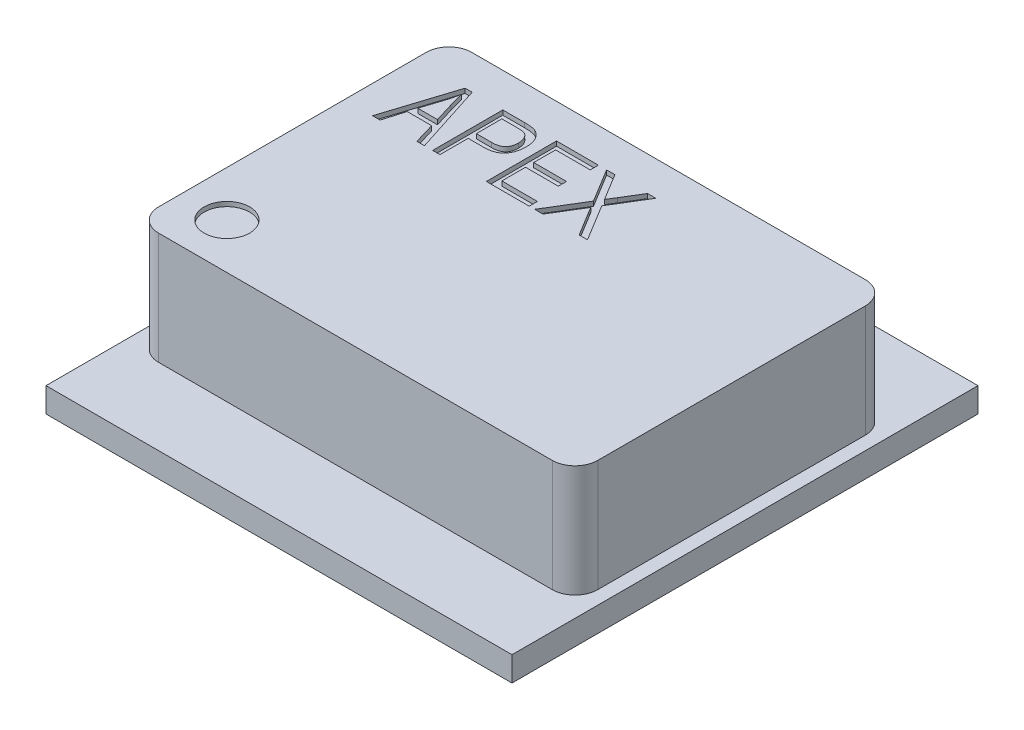
SolidWorks part; units mm, degrees
ref_plane "Front Plane" through (0, 0, 0) normal (0, 0, 1) x (1, 0, 0)
ref_plane "Top Plane" through (0, 0, 0) normal (0, 1, 0) x (1, 0, 0)
ref_plane "Right Plane" through (0, 0, 0) normal (1, 0, 0) x (0, 0, -1)
sketch "Sketch1" plane through (0, 0, 0) normal (0, 1, 0) x (1, 0, 0)
  line L1 (-5.12, -5.12) -> (5.12, -5.12)
  line L2 (-5.12, -5.12) -> (-5.12, 5.12)
  line L3 (-5.12, 5.12) -> (5.12, 5.12)
  line L4 (5.12, -5.12) -> (5.12, 5.12)
  line L5 (-5.12, -5.12) -> (5.12, 5.12) construction
  line L6 (-5.12, 5.12) -> (5.12, -5.12) construction
  point P0 (0, 0)
  dimension "D1" = 10.24
  dimension "D2" = 10.24
extrude "Boss-Extrude1" add sketch "Sketch1" along normal blind 0.54
sketch "Sketch2" plane through (0, 0.54, 0) normal (0, 1, 0) x (1, 0, 0)
  line L1 (-4.825, -3.44) -> (4.825, -3.44)
  line L2 (-4.825, -3.44) -> (-4.825, 3.44)
  line L3 (-4.825, 3.44) -> (4.825, 3.44)
  line L4 (4.825, -3.44) -> (4.825, 3.44)
  line L5 (-4.825, -3.44) -> (4.825, 3.44) construction
  line L6 (-4.825, 3.44) -> (4.825, -3.44) construction
  point P0 (0, 0)
  dimension "D1" = 9.65
  dimension "D2" = 6.88
extrude "Boss-Extrude2" add sketch "Sketch2" along normal blind 2.46
fillet "Fillet1" radius 0.5 4 edges at (-4.825, 1.77, 3.44) (4.825, 1.77, 3.44) (4.825, 1.77, -3.44) (-4.825, 1.77, -3.44)
sketch "Sketch3" plane through (0, 3, 0) normal (0, 1, 0) x (1, 0, 0)
  line L0 (-4.325, -3.44) -> (4.325, -3.44) construction
  line L1 (-4.825, 2.94) -> (-4.825, -2.94) construction
  circle A0 centre (-3.825, -2.44) radius 0.5
  dimension "D1" = 1
  dimension "D2" = 1
  dimension "D3" = 1
extrude "Cut-Extrude1" cut sketch "Sketch3" against normal blind 0.1
sketch "Sketch4" plane through (0, 3, 0) normal (0, 1, 0) x (1, 0, 0)
  line L0 (-4.2089, 1.1442) -> (3.3596, 1.1442) construction
  text T0 "APEX" font "Arial Narrow" height in points 6
extrude "Cut-Extrude2" cut sketch "Sketch4" against normal blind 0.1
